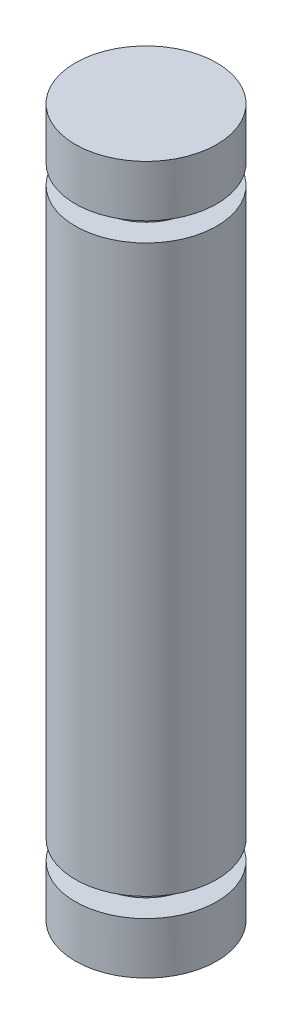
SolidWorks part; units mm, degrees
ref_plane "Front Plane" through (0, 0, 0) normal (0, 0, 1) x (1, 0, 0)
ref_plane "Top Plane" through (0, 0, 0) normal (0, 1, 0) x (1, 0, 0)
ref_plane "Right Plane" through (0, 0, 0) normal (1, 0, 0) x (0, 0, -1)
sketch "Sketch2" plane through (0, 0, 0) normal (0, 1, 0) x (1, 0, 0)
  circle A0 centre (0, 0) radius 2.5
  dimension "D1" = 5
extrude "Boss-Extrude1" add sketch "Sketch2" along normal blind 25
sketch "Sketch3" plane through (0, 0, 0) normal (1, 0, 0) x (0, 0, -1)
  line L0 (-2.5, 0) -> (-2.5, 1.82) construction
  line L1 (-2.5, 25) -> (-2.5, 0) construction
  line L2 (-2.5, 1.82) -> (-1.6, 1.82)
  line L3 (-1.6, 1.82) -> (-1.6, 2.5)
  line L4 (-1.6, 2.5) -> (-2.5, 2.5)
  line L5 (-2.5, 2.5) -> (-2.5, 1.82)
  line L6 (2.5, 0) -> (2.5, 1.82) construction
  line L7 (2.5, 0) -> (2.5, 25) construction
  line L8 (2.5, 1.82) -> (1.6, 1.82) construction
  line L9 (1.6, 1.82) -> (1.6, 2.5) construction
  line L10 (1.6, 2.5) -> (2.5, 2.5) construction
  line L11 (2.5, 2.5) -> (2.5, 1.82) construction
  line L12 (0, 0) -> (0, 25) construction
  line L13 (2.5, 25) -> (-2.5, 25) construction
  line L14 (-2.5, 12.5) -> (2.5, 12.5) construction
  line L15 (-2.5, 25) -> (-2.5, 23.18) construction
  line L16 (-2.5, 22.5) -> (-2.5, 23.18)
  line L17 (-1.6, 22.5) -> (-2.5, 22.5)
  line L18 (-1.6, 23.18) -> (-1.6, 22.5)
  line L19 (-2.5, 23.18) -> (-1.6, 23.18)
  dimension "D1" = 2.5
  dimension "D2" = 3.2
  dimension "D3" = 0.68
revolve "Cut-Revolve1" cut sketch "Sketch3" angle 360 about L12
